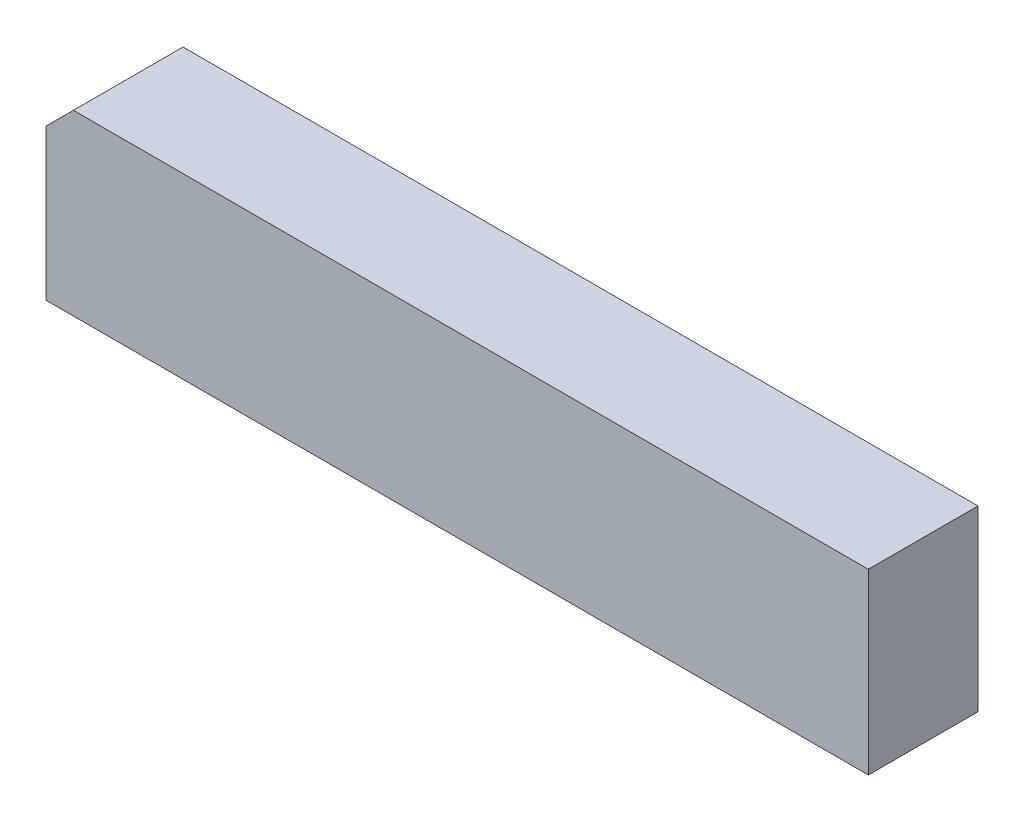
SolidWorks part; units mm, degrees
ref_plane "Ebene vorne" through (0, 0, 0) normal (0, 0, 1) x (1, 0, 0)
ref_plane "Ebene oben" through (0, 0, 0) normal (0, 1, 0) x (1, 0, 0)
ref_plane "Ebene rechts" through (0, 0, 0) normal (1, 0, 0) x (0, 0, -1)
sketch "Skizze1" plane through (0, 0, 0) normal (0, 0, 1) x (1, 0, 0)
  line L0 (0, 5.5) -> (1, 6.5)
  line L1 (0, 0) -> (30, 0)
  line L2 (0, 0) -> (0, 5.5)
  line L3 (1, 6.5) -> (30, 6.5)
  line L4 (30, 0) -> (30, 6.5)
  point P2 (0, 6.5)
  dimension "D1" = 6.5
  dimension "D2" = 30
extrude "Aufsatz-Linear austragen1" add sketch "Skizze1" along normal blind 4
